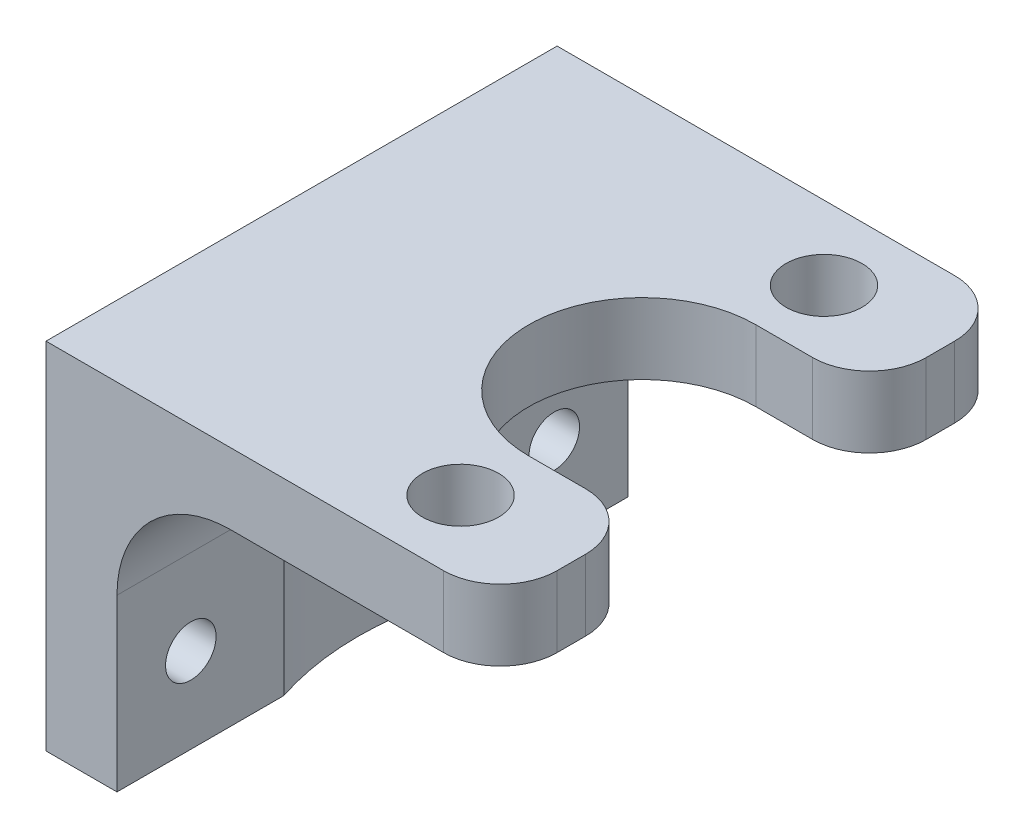
SolidWorks part; units mm, degrees
ref_plane "Front Plane" through (0, 0, 0) normal (0, 0, 1) x (1, 0, 0)
ref_plane "Top Plane" through (0, 0, 0) normal (0, 1, 0) x (1, 0, 0)
ref_plane "Right Plane" through (0, 0, 0) normal (1, 0, 0) x (0, 0, -1)
sketch "Sketch1" plane through (0, 0, 0) normal (0, 1, 0) x (1, 0, 0)
  line L1 (-10.16, -11.43) -> (10.16, -11.43)
  line L2 (-10.16, -11.43) -> (-10.16, 11.43)
  line L3 (-10.16, 11.43) -> (10.16, 11.43)
  line L4 (10.16, -11.43) -> (10.16, 11.43)
  line L5 (-10.16, -11.43) -> (10.16, 11.43) construction
  line L6 (-10.16, 11.43) -> (10.16, -11.43) construction
  point P0 (0, 0)
  dimension "D1" = 20.32
  dimension "D2" = 22.86
extrude "Boss-Extrude1" add sketch "Sketch1" along normal blind 3.175
fillet "Fillet1" radius 2.54 1 edges at (10.16, 1.5875, -11.43)
fillet "Fillet2" radius 2.54 1 edges at (10.16, 1.5875, 11.43)
sketch "Sketch2" plane through (0, 0, 0) normal (0, -1, 0) x (1, 0, 0)
  line L0 (-10.16, -11.43) -> (-10.16, 11.43) construction
  line L1 (7.62, -11.43) -> (-10.16, -11.43) construction
  line L2 (5.08, -5.08) -> (10.16, -5.08)
  line L3 (10.16, 8.89) -> (10.16, -8.89) construction
  line L4 (5.08, 5.08) -> (10.16, 5.08)
  line L5 (10.16, 5.08) -> (10.16, -5.08)
  arc A0 (5.08, 5.08) -> (5.08, -5.08) centre (5.08, 0) ccw
  dimension "D1" = 10.16
  dimension "D2" = 15.24
  dimension "D3" = 11.43
  dimension "D4" = 5.08
extrude "Cut-Extrude2" cut sketch "Sketch2" against normal through all
fillet "Fillet3" radius 2.54 1 edges at (10.16, 1.5875, 5.08)
fillet "Fillet4" radius 2.54 1 edges at (10.16, 1.5875, -5.08)
sketch "Sketch4" plane through (0, 0, 0) normal (0, -1, 0) x (1, 0, 0)
  line L0 (7.62, -11.43) -> (-10.16, -11.43) construction
  line L1 (-10.16, 11.43) -> (-6.985, 11.43)
  line L2 (-10.16, 11.43) -> (-10.16, -11.43)
  line L3 (-10.16, -11.43) -> (-6.985, -11.43)
  line L4 (-6.985, 11.43) -> (-6.985, -11.43)
  dimension "D1" = 3.175
extrude "Boss-Extrude2" add sketch "Sketch4" along normal blind 12.7
fillet "Fillet6" radius 5.08 2 edges
sketch "Sketch3" plane through (0, 0, 0) normal (0, -1, 0) x (1, 0, 0)
  line L0 (7.62, -11.43) -> (-1.905, -11.43) construction
  line L1 (-1.905, 11.43) -> (7.62, 11.43) construction
  line L2 (-10.16, -11.43) -> (-10.16, 11.43) construction
  circle A0 centre (5.08, 8.128) radius 0.9525
  circle A1 centre (5.08, -8.128) radius 0.9525
  dimension "D1" = 16.256
  dimension "D4" = 1.905
  dimension "D5" = 1.905
  dimension "D2" = 3.302
  dimension "D3" = 3.302
  dimension "D6" = 15.24
sketch "Sketch5" plane through (0, 0, 0) normal (0, -1, 0) x (1, 0, 0)
  line L0 (-10.16, 11.43) -> (-10.16, -11.43) construction
  line L1 (7.62, -11.43) -> (-1.905, -11.43) construction
  circle A0 centre (5.08, 0) radius 12.7
  dimension "D1" = 25.4
  dimension "D2" = 15.24
  dimension "D3" = 11.43
extrude "Cut-Extrude4" cut sketch "Sketch5" along normal through all
sketch "Sketch6" plane through (-6.985, 0, 0) normal (1, 0, 0) x (0, 0, -1)
  line L0 (11.43, -12.7) -> (11.43, -5.08) construction
  line L1 (-11.43, -12.7) -> (-11.43, -5.08) construction
  line L2 (11.43, -12.7) -> (3.9656, -12.7) construction
  circle A0 centre (-8.128, -8.89) radius 1.651
  circle A1 centre (8.128, -8.89) radius 1.651
  point P6 (-11.43, -8.89)
  dimension "D1" = 3.302
  dimension "D2" = 3.302
  dimension "D3" = 16.256
  dimension "D4" = 3.302
  dimension "D5" = 3.302
  dimension ".2" = 3.81
hole_wizard "#4-40 Tapped Hole3" positions "Sketch10" profile "Sketch9" tap size "#4-40" standard "ANSI Inch" end condition through all
sketch "Sketch10" plane through (-6.985, 0, 0) normal (1, 0, 0) x (0, 0, -1)
  point P0 (-8.128, -8.89)
  point P3 (8.128, -8.89)
sketch "Sketch9" plane through (-6.985, -8.89, 8.128) normal (0, 1, 0) x (0, 0, -1)
  line L0 (0, 0) -> (0, 3.175)
  line L1 (0, 3.175) -> (1.1303, 3.175)
  line L2 (1.1303, 3.175) -> (1.1303, 0)
  line L5 (1.1303, 0) -> (0, 0)
  line L11 (0, -6.35) -> (0, 107.95) construction
  dimension "Thru Tap Drill Dia." = 2.2606
  dimension "Thru Tap Drill Depth" = 3.175
cosmetic thread "Hole Thread1" parameters "D2"=2.8448
cosmetic thread "Hole Thread2" parameters "D2"=2.8448
hole_wizard "M3 Clearance Hole1" positions "Sketch13" profile "Sketch11" hole size "M3" standard "ANSI Metric" end condition through all
sketch "Sketch13" plane through (0, 0, 0) normal (0, -1, 0) x (-1, 0, 0)
  point P0 (-5.08, -8.128)
  point P3 (-5.08, 8.128)
sketch "Sketch11" plane through (5.08, 0, 8.128) normal (1, 0, 0) x (0, 0, -1)
  line L0 (0, 0) -> (0, 3.175)
  line L1 (0, 3.175) -> (1.7, 3.175)
  line L2 (1.7, 3.175) -> (1.7, 0)
  line L5 (1.7, 0) -> (0, 0)
  line L11 (0, -6.35) -> (0, 107.95) construction
  dimension "Thru Hole Dia." = 3.4
  dimension "Thru Hole Depth" = 3.175
